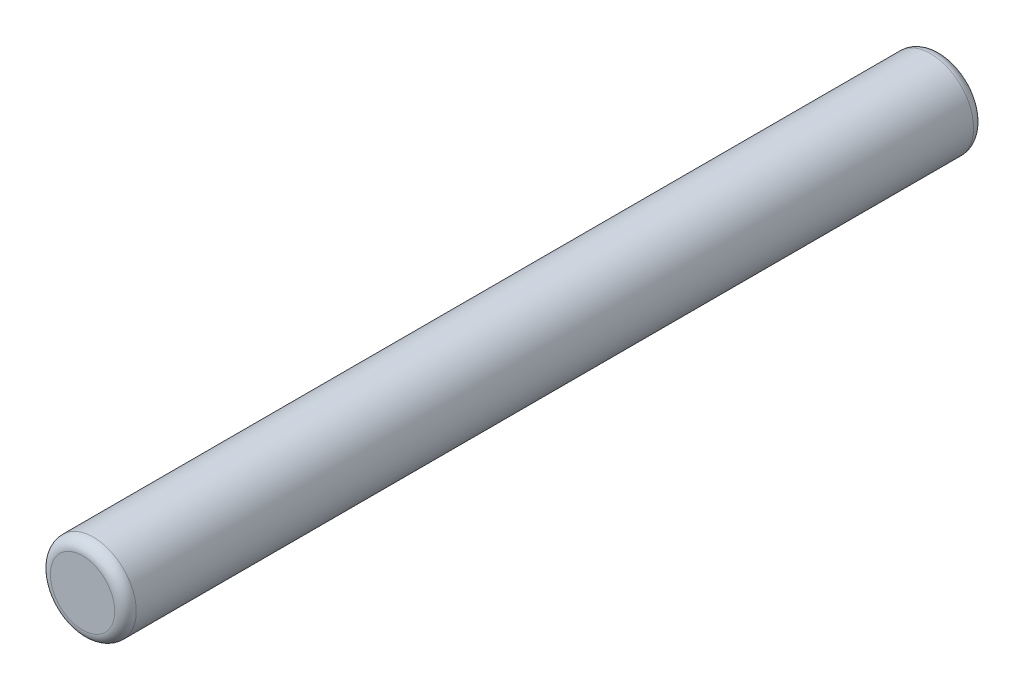
SolidWorks part; units mm, degrees
ref_plane "前视" through (0, 0, 0) normal (0, 0, 1) x (1, 0, 0)
ref_plane "上视" through (0, 0, 0) normal (0, 1, 0) x (1, 0, 0)
ref_plane "右视" through (0, 0, 0) normal (1, 0, 0) x (0, 0, -1)
sketch "草图1" plane through (0, 0, 0) normal (0, 0, 1) x (1, 0, 0)
  circle A0 centre (0, 0) radius 2
extrude "凸台-拉伸1" add sketch "草图1" along normal blind 40
fillet "圆角1" radius 0.5 2 edges at (2, 0, 40) (2, 0, 0)
